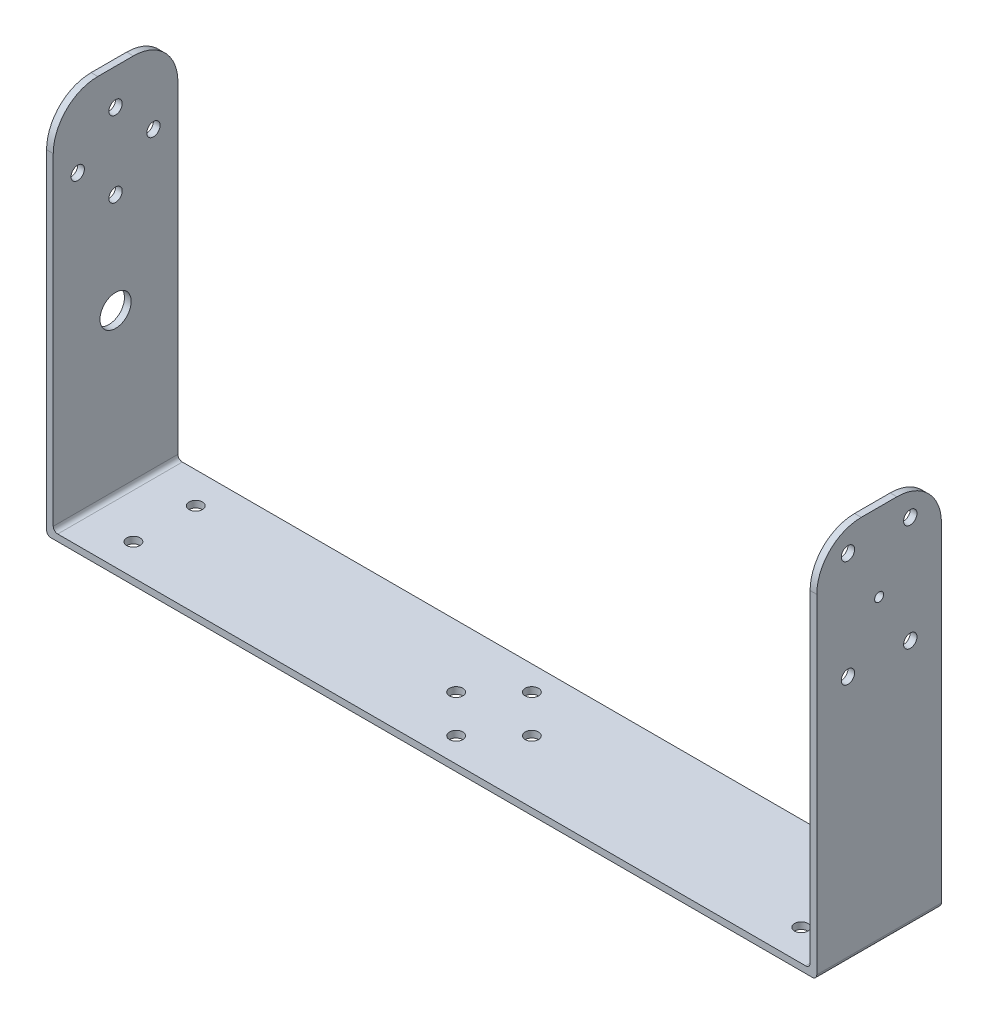
SolidWorks part; units mm, degrees
ref_plane "Front Plane" through (0, 0, 0) normal (0, 0, 1) x (1, 0, 0)
ref_plane "Top Plane" through (0, 0, 0) normal (0, 1, 0) x (1, 0, 0)
ref_plane "Right Plane" through (0, 0, 0) normal (1, 0, 0) x (0, 0, -1)
sketch "Sketch1" plane through (0, 0, 0) normal (0, 1, 0) x (1, 0, 0)
  line L1 (0, 0) -> (170, 0)
  line L2 (0, 0) -> (0, 28)
  line L3 (0, 28) -> (170, 28)
  line L4 (170, 0) -> (170, 28)
  dimension "D1" = 28
  dimension "D2" = 170
extrude "Boss-Extrude1" add sketch "Sketch1" along normal blind 1.5
sketch "Sketch2" plane through (0, 0, 0) normal (1, 0, 0) x (0, 0, -1)
  line L1 (28, 0) -> (0, 0)
  line L2 (28, 0) -> (28, 85)
  line L3 (28, 85) -> (0, 85)
  line L4 (0, 0) -> (0, 85)
  dimension "D1" = 85
extrude "Boss-Extrude2" add sketch "Sketch2" against normal blind 1.5
fillet "Fillet2" radius 10 2 edges at (-0.75, 85, -28) (-0.75, 85, 0)
fillet "Fillet3" radius 1 1 edges at (-1.5, 0, -14)
fillet "Fillet4" radius 1 1 edges
sketch "Sketch5" plane through (0, 0, 0) normal (1, 0, 0) x (0, 0, -1)
  line L0 (18, 85) -> (10, 85) construction
  line L1 (0, 75) -> (0, 2.5) construction
  line L2 (28, 2.5) -> (28, 75) construction
  circle A0 centre (14, 77) radius 1.5
  circle A1 centre (14, 60) radius 1.5
  circle A2 centre (22.5, 68.5) radius 1.5
  circle A3 centre (5.5, 68.5) radius 1.5
  point P8 (14, 85)
  dimension "D1" = 8
  dimension "D2" = 14
  dimension "D3" = 17
  dimension "D4" = 14
  dimension "D7" = 5.5
  dimension "D8" = 16.5
  dimension "D9" = 16.5
  dimension "D10" = 5.5
extrude "Cut-Extrude2" cut sketch "Sketch5" against normal blind 15 and the other way blind 15
sketch "Sketch7" plane through (0, 0, 0) normal (1, 0, 0) x (0, 0, -1)
  circle A0 centre (14, 37.5) radius 3.5
extrude "Cut-Extrude3" cut sketch "Sketch7" against normal blind 15 and the other way blind 15
sketch "Sketch8" plane through (0, 1.5, 0) normal (0, 1, 0) x (1, 0, 0)
  line L0 (1, 28) -> (1, 0) construction
  line L2 (170, 28) -> (1, 28) construction
  line L3 (1, 0) -> (170, 0) construction
  circle A1 centre (161, 7) radius 1.5
  circle A2 centre (11, 21) radius 1.5
  circle A3 centre (11, 7) radius 1.5
  circle A4 centre (161, 21) radius 1.5
  dimension "D3" = 7
  dimension "D4" = 7
  dimension "D1" = 7
  dimension "D2" = 7
  dimension "D5" = 150
  dimension "D6" = 10
  dimension "D7" = 14
  dimension "D8" = 150
  dimension "D9" = 10
extrude "Cut-Extrude4" cut sketch "Sketch8" against normal blind 15 and the other way blind 15
sketch "Sketch11" plane through (170, 0, 0) normal (1, 0, 0) x (0, 0, -1)
  line L1 (28, 0) -> (0, 0)
  line L2 (28, 0) -> (28, 85)
  line L3 (28, 85) -> (0, 85)
  line L4 (0, 0) -> (0, 85)
  circle A0 centre (14, 67.5) radius 1
  dimension "D3" = 14
  dimension "D1" = 85
  dimension "D2" = 28
  dimension "D4" = 17.5
extrude "Boss-Extrude5" add sketch "Sketch11" along normal blind 1.5
fillet "Fillet5" radius 1 1 edges
fillet "Fillet6" radius 1 1 edges at (171.5, 0, -14)
fillet "Fillet7" radius 10 1 edges at (170.75, 85, 0)
fillet "Fillet8" radius 10 1 edges at (170.75, 85, -28)
sketch "Sketch12" plane through (170, 0, 0) normal (-1, 0, 0) x (0, 0, 1)
  line L4 (-28, 2.5) -> (-28, 75) construction
  line L5 (0, 75) -> (0, 2.5) construction
  circle A0 centre (-21, 79.5) radius 1.5
  circle A1 centre (-7, 79.5) radius 1.5
  circle A2 centre (-7, 55.5) radius 1.5
  circle A3 centre (-21, 55.5) radius 1.5
  circle A4 centre (-14, 67.5) radius 1 construction
  dimension "D1" = 12
  dimension "D2" = 7
  dimension "D3" = 12
  dimension "D4" = 7
  dimension "D5" = 12
  dimension "D6" = 7
  dimension "D7" = 7
  dimension "D8" = 12
extrude "Cut-Extrude5" cut sketch "Sketch12" against normal blind 10 and the other way blind 10
sketch "Sketch13" plane through (0, 1.5, 0) normal (0, 1, 0) x (1, 0, 0)
  line L0 (169, 28) -> (1, 28) construction
  line L1 (169, 0) -> (169, 28) construction
  line L4 (1, 0) -> (169, 0) construction
  circle A0 centre (85, 22.5) radius 1.5
  circle A1 centre (85, 5.5) radius 1.5
  circle A2 centre (93.5, 14) radius 1.5
  circle A3 centre (76.5, 14) radius 1.5
  point P10 (169, 14)
  dimension "D1" = 14
  dimension "D2" = 14
  dimension "D3" = 17
  dimension "D4" = 75.5
  dimension "D5" = 8.5
  dimension "D6" = 8.5
  dimension "D7" = 17
  dimension "D8" = 5.5
extrude "Cut-Extrude6" cut sketch "Sketch13" against normal blind 10 and the other way blind 10
